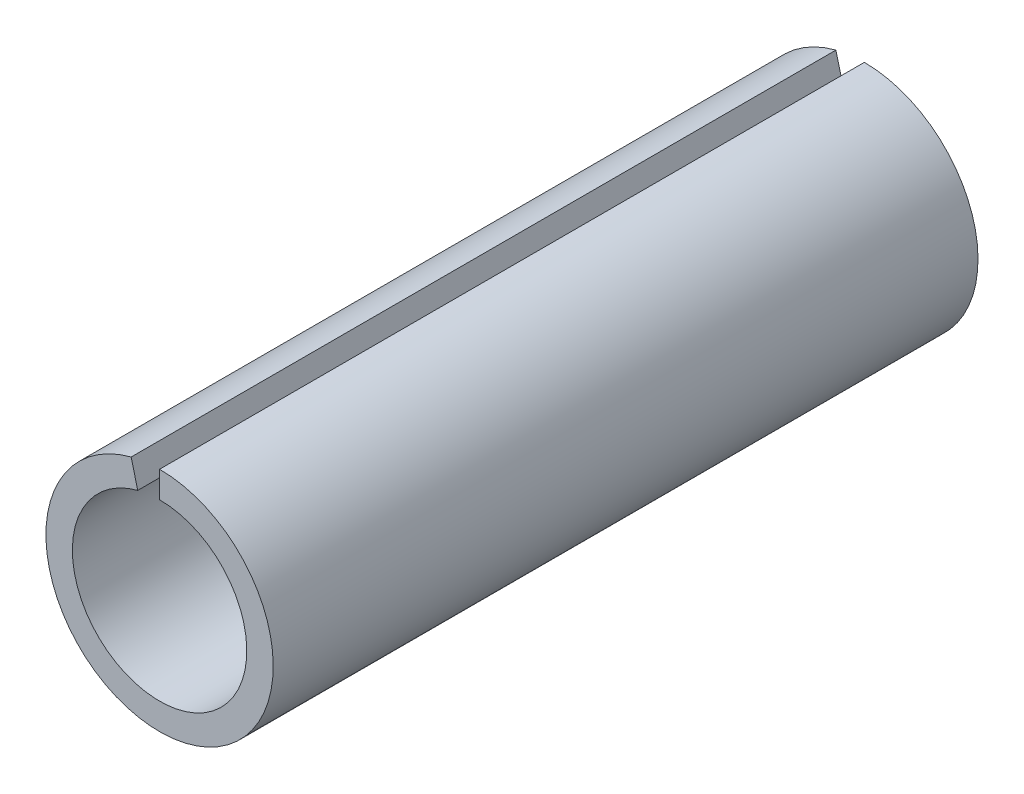
SolidWorks part; units mm, degrees
ref_plane "Plan de face" through (0, 0, 0) normal (0, 0, 1) x (1, 0, 0)
ref_plane "Plan de dessus" through (0, 0, 0) normal (0, 1, 0) x (1, 0, 0)
ref_plane "Plan de droite" through (0, 0, 0) normal (1, 0, 0) x (0, 0, -1)
sketch "Esquisse1" plane through (0, 0, 0) normal (0, 0, 1) x (1, 0, 0)
  line L0 (-1.6144, 6.2447) -> (-1.239, 4.7924)
  line L1 (0, 4.95) -> (0, 6.45)
  arc A0 (-1.239, 4.7924) -> (0, 4.95) centre (0, 0) ccw
  arc A1 (-1.6144, 6.2447) -> (0, 6.45) centre (0, 0) ccw
  dimension "D1" = 9.9
  dimension "D2" = 1.5
extrude "Boss.-Extru.1" add sketch "Esquisse1" along normal blind 40
